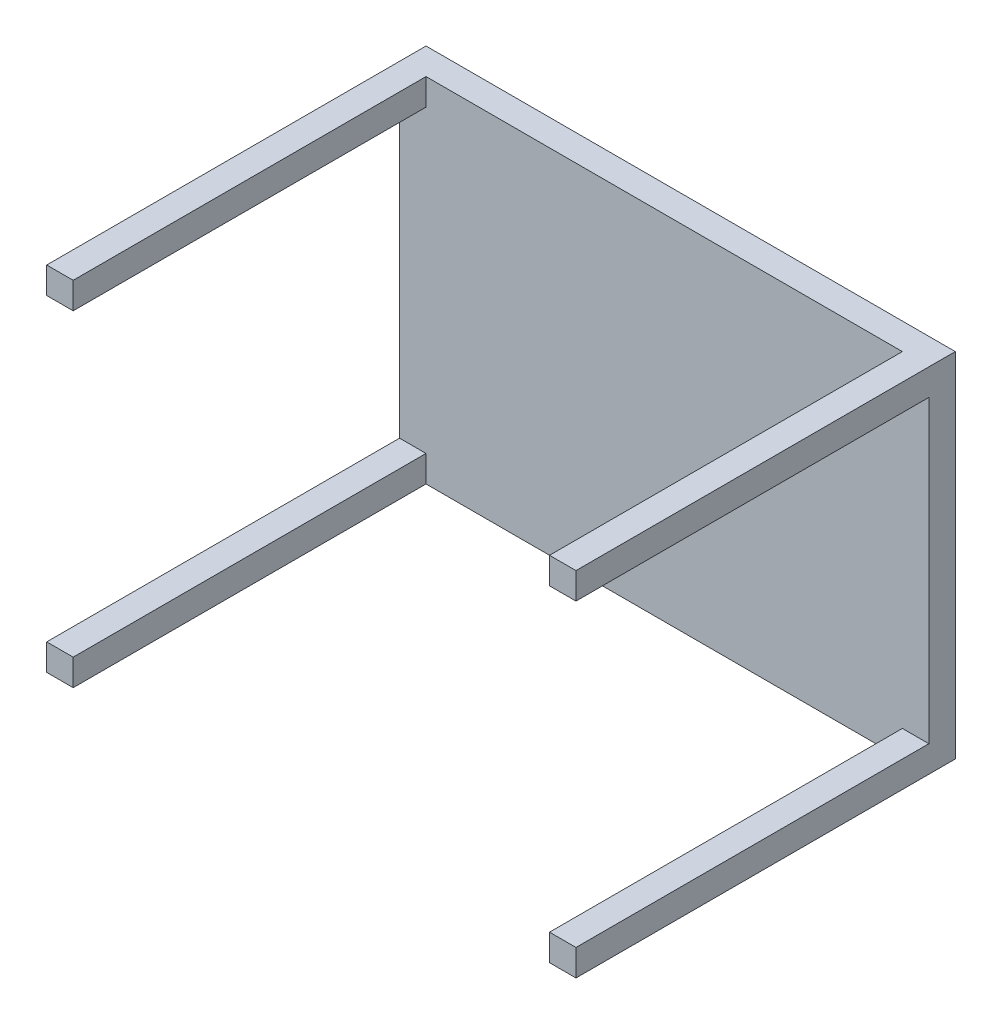
SolidWorks part; units mm, degrees
ref_plane "Front Plane" through (0, 0, 0) normal (0, 0, 1) x (1, 0, 0)
ref_plane "Top Plane" through (0, 0, 0) normal (0, 1, 0) x (1, 0, 0)
ref_plane "Right Plane" through (0, 0, 0) normal (1, 0, 0) x (0, 0, -1)
sketch "Sketch1" plane through (0, 0, 0) normal (0, 0, 1) x (1, 0, 0)
  line L1 (300, -200) -> (-300, -200)
  line L2 (300, -200) -> (300, 200)
  line L3 (300, 200) -> (-300, 200)
  line L4 (-300, -200) -> (-300, 200)
  line L5 (300, -200) -> (-300, 200) construction
  line L6 (300, 200) -> (-300, -200) construction
  point P0 (0, 0)
  dimension "D1" = 400
  dimension "D2" = 600
extrude "Boss-Extrude1" add sketch "Sketch1" along normal blind 30
sketch "Sketch2" plane through (0, 0, 30) normal (0, 0, 1) x (1, 0, 0)
  line L0 (270, 200) -> (300, 200)
  line L1 (-300, 200) -> (-270, 200)
  line L2 (-300, 200) -> (-300, 170)
  line L3 (-300, 170) -> (-270, 170)
  line L4 (-270, 200) -> (-270, 170)
  line L5 (270, 200) -> (270, 170)
  line L6 (270, 170) -> (300, 170)
  line L7 (300, 200) -> (300, 170)
  line L8 (270, -170) -> (300, -170)
  line L9 (270, -170) -> (270, -200)
  line L10 (270, -200) -> (300, -200)
  line L11 (300, -170) -> (300, -200)
  line L12 (-300, -170) -> (-270, -170)
  line L13 (-300, -170) -> (-300, -200)
  line L14 (-300, -200) -> (-270, -200)
  line L15 (-270, -170) -> (-270, -200)
  dimension "D1" = 30
  dimension "D2" = 30
  dimension "D3" = 2
  dimension "D4" = 2
extrude "Boss-Extrude2" add sketch "Sketch2" along normal blind 400
